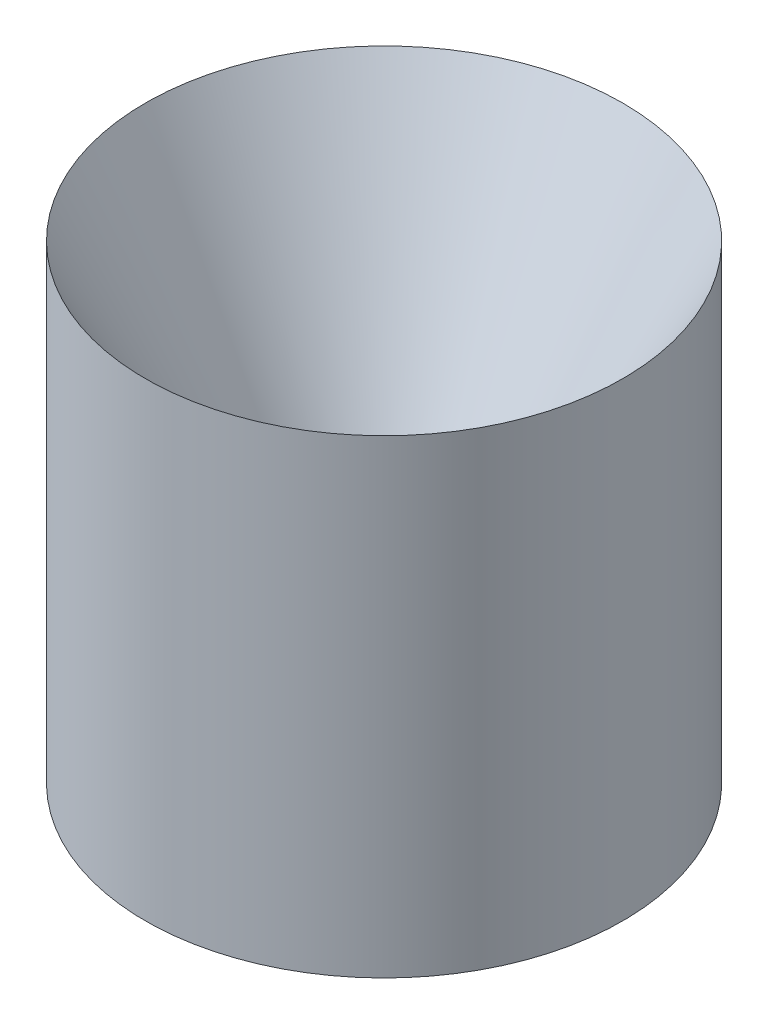
SolidWorks part; units mm, degrees
material "PP Copolymer"
ref_plane "Front Plane" through (0, 0, 0) normal (0, 0, 1) x (1, 0, 0)
ref_plane "Top Plane" through (0, 0, 0) normal (0, 1, 0) x (1, 0, 0)
ref_plane "Right Plane" through (0, 0, 0) normal (1, 0, 0) x (0, 0, -1)
sketch "Sketch1" plane through (0, 0, 0) normal (0, 0, 1) x (1, 0, 0)
  line L0 (0, 0) -> (0, 0.035) construction
  line L1 (-13.335, 0) -> (13.335, 0) construction
  line L2 (-13.335, 0) -> (-13.335, 15.2802)
  line L3 (-13.335, 0) -> (-38.735, 0)
  line L4 (-38.735, 0) -> (-38.735, 76.2)
  line L6 (-13.335, 15.2802) -> (-6.5794, 15.2802)
  line L8 (-6.5794, 15.2802) -> (-38.735, 76.2)
  line L9 (-6.5794, 15.2802) -> (0, 15.2802) construction
  point P7 (0, 0)
  dimension "D1" = 6.5794
revolve "Revolve1" add sketch "Sketch1" angle 360 about L0
